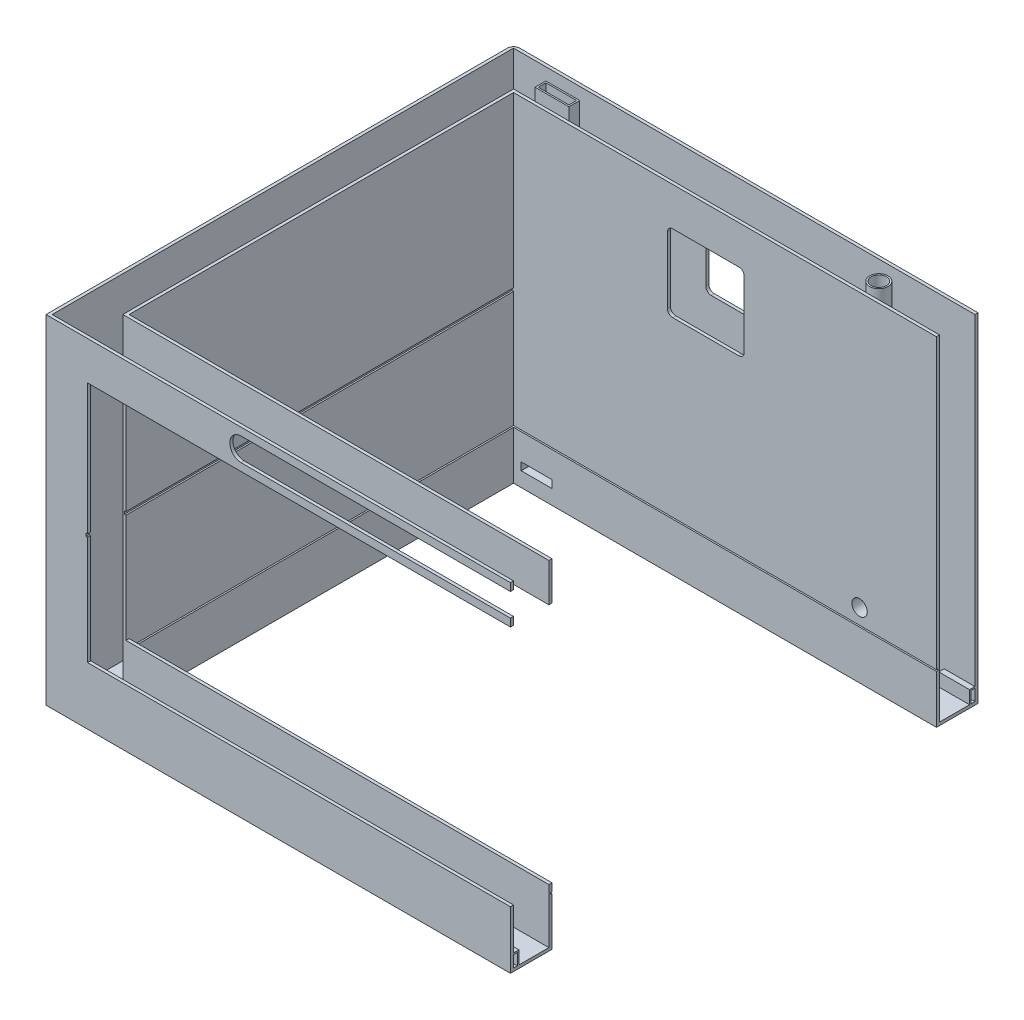
SolidWorks part; units mm, degrees
material "PVC Rigid"
ref_plane "Front Plane" through (0, 0, 0) normal (0, 0, 1) x (1, 0, 0)
ref_plane "Top Plane" through (0, 0, 0) normal (0, 1, 0) x (1, 0, 0)
ref_plane "Right Plane" through (0, 0, 0) normal (1, 0, 0) x (0, 0, -1)
sketch "Sketch1" plane through (0, 0, 0) normal (0, 1, 0) x (1, 0, 0)
  line L0 (0, -300) -> (0, 300) construction
  line L1 (0, 300) -> (-600, 300)
  line L2 (-600, 300) -> (-600, -300)
  line L3 (-600, -300) -> (0, -300)
  line L4 (0, -300) -> (0, -304)
  line L5 (0, -304) -> (-604, -304)
  line L6 (-604, -304) -> (-604, 304)
  line L7 (-604, 304) -> (0, 304)
  line L8 (0, 304) -> (0, 300)
  point P4 (0, 0)
extrude "Boss-Extrude1" add sketch "Sketch1" along normal blind 440
sketch "Sketch2" plane through (0, 0, 0) normal (0, 1, 0) x (1, 0, 0)
  line L0 (0, 0) -> (0, 250) construction
  line L1 (0, 250) -> (-550, 250)
  line L2 (-550, 250) -> (-550, -250)
  line L3 (-550, -250) -> (0, -250)
  line L4 (0, -250) -> (0, -254)
  line L5 (0, -254) -> (-554, -254)
  line L6 (-554, -254) -> (-554, 254)
  line L7 (-554, 254) -> (0, 254)
  line L8 (0, 254) -> (0, 250)
extrude "Boss-Extrude2" add sketch "Sketch2" along normal blind 440 separate body
sketch "Sketch3" plane through (0, 0, 0) normal (0, 1, 0) x (1, 0, 0)
  line L0 (0, -254) -> (0, -300)
  line L1 (0, -300) -> (-600, -300)
  line L2 (-600, -300) -> (-600, 300)
  line L3 (-600, 300) -> (0, 300)
  line L4 (0, 300) -> (0, 254)
  line L5 (0, 254) -> (-554, 254)
  line L6 (-554, 254) -> (-554, -254)
  line L7 (-554, -254) -> (0, -254)
extrude "Boss-Extrude3" add sketch "Sketch3" along normal blind 4
sketch "Sketch4" plane through (-550, 0, 0) normal (1, 0, 0) x (0, 0, -1)
  line L0 (0, 440) -> (0, 220) construction
  line L1 (-250, 440) -> (250, 440) construction
  line L2 (-250, 220) -> (250, 220)
  line L3 (250, 440) -> (250, 0) construction
  line L4 (-250, 220) -> (-250, 216)
  line L5 (-250, 440) -> (-250, 0) construction
  line L6 (-250, 216) -> (250, 216)
  line L7 (250, 216) -> (250, 220)
  line L8 (-250, 440) -> (-250, 0) construction
  point P10 (0, 220)
extrude "Cut-Extrude1" cut sketch "Sketch4" against normal blind 2
ref_plane "Plane1" through (0, 64, 0) normal (0, 1, 0) x (1, 0, 0)
sketch "Sketch7" plane through (0, 64, 0) normal (0, 1, 0) x (1, 0, 0)
  line L0 (-550, 250) -> (0, 250)
  line L1 (0, 250) -> (0, 252)
  line L2 (0, 250) -> (0, 254) construction
  line L3 (0, 252) -> (-552, 252)
  line L4 (-552, 252) -> (-552, -252)
  line L5 (-552, -252) -> (0, -252)
  line L6 (0, -254) -> (0, -250) construction
  line L7 (0, -252) -> (0, -250)
  line L8 (0, -250) -> (-550, -250)
  line L9 (-550, -250) -> (-550, 250)
extrude "Cut-Extrude3" cut sketch "Sketch7" against normal blind 1 and the other way blind 1
ref_plane "Plane2" through (0, 42, 0) normal (0, 1, 0) x (1, 0, 0)
sketch "Sketch10" plane through (0, 0, 304) normal (0, 0, 1) x (1, 0, 0)
  line L0 (0, 440) -> (0, 0) construction
  line L1 (-604, 440) -> (0, 440) construction
  line L2 (0, 390) -> (-550, 390)
  line L3 (-550, 390) -> (-550, 220)
  line L4 (-550, 220) -> (-552, 220)
  line L5 (-552, 220) -> (-552, 216)
  line L8 (-550, 75) -> (0, 75)
  line L9 (0, 75) -> (0, 390)
  line L10 (-552, 216) -> (-550, 216)
  line L11 (-550, 216) -> (-550, 75)
  point P0 (0, 390)
  dimension "D1" = 50
extrude "Cut-Extrude6" cut sketch "Sketch10" against normal up to vertex (54 mm away)
ref_plane "Plane3" through (0, 0, 0) normal (1, 0, 0) x (0, 0, -1)
sketch "Sketch11" plane through (0, 0, 0) normal (1, 0, 0) x (0, 0, -1)
  line L9 (-300, 4) -> (-254, 4) construction
  line L10 (-300, 75) -> (-300, 4) construction
  line L11 (-295, 4) -> (-295, 19)
  line L12 (-295, 19) -> (-300, 19)
  line L13 (-300, 19) -> (-300, 21)
  line L14 (-300, 440) -> (-300, 4) construction
  line L15 (-300, 21) -> (-293, 21)
  line L16 (-293, 21) -> (-293, 4)
  line L17 (-293, 4) -> (-295, 4)
  point P0 (-295, 4)
  dimension "D1" = 5
extrude "Boss-Extrude6" add sketch "Sketch11" against normal blind 40
sketch "Sketch12" plane through (0, 0, 0) normal (1, 0, 0) x (0, 0, -1)
  line L0 (254, 4) -> (300, 4) construction
  line L1 (300, 440) -> (300, 4) construction
  line L2 (295, 4) -> (293, 4)
  line L3 (300, 4) -> (-300, 4) construction
  line L4 (293, 4) -> (293, 21)
  line L5 (293, 21) -> (300, 21)
  line L6 (300, 21) -> (300, 19)
  line L7 (300, 19) -> (295, 19)
  line L8 (295, 19) -> (295, 4)
  point P0 (295, 4)
  dimension "D1" = 5
extrude "Boss-Extrude5" add sketch "Sketch12" against normal blind 40
sketch "Sketch13" plane through (0, 0, 304) normal (0, 0, 1) x (1, 0, 0)
  line L1 (0, 400) -> (0, 430)
  line L4 (0, 430) -> (-350, 430)
  line L9 (0, 440) -> (0, 390) construction
  line L10 (0, 400) -> (-350, 400)
  arc A0 (-350, 430) -> (-350, 400) centre (-350, 415) ccw
  point P5 (0, 415)
extrude "Cut-Extrude9" cut sketch "Sketch13" against normal blind 4 contours L4 A0 L10 L1
sketch "Sketch14" plane through (0, 0, -250) normal (0, 0, 1) x (1, 0, 0)
  line L0 (-550, 440) -> (0, 440) construction
  line L1 (-550, 440) -> (-550, 220) construction
  line L3 (-350, 290) -> (-250, 290)
  line L4 (-350, 290) -> (-350, 390)
  line L5 (-350, 390) -> (-250, 390)
  line L6 (-250, 290) -> (-250, 390)
  line L7 (-350, 290) -> (-250, 390) construction
  line L8 (-350, 390) -> (-250, 290) construction
  point P0 (-300, 340)
  point P5 (-300, 340)
  dimension "D1" = 100
  dimension "D2" = 250
extrude "Cut-Extrude10" cut sketch "Sketch14" against normal through all contours L5 L6 L3 L4
fillet "Fillet1" radius 7 8 edges at (-250, 290, -302) (-250, 290, -252) (-350, 290, -302) (-350, 290, -252) (-250, 390, -252) (-250, 390, -302) (-350, 390, -252) (-350, 390, -302)
fillet "Fillet2" radius 8 1 edges at (-604, 220, -304)
sketch "Sketch15" plane through (0, 0, 0) normal (0, -1, 0) x (1, 0, 0)
  line L0 (-604, -296) -> (-604, 304) construction
  line L1 (-604, 304) -> (0, 304) construction
  line L2 (-600, 300) -> (-600, 288)
  line L3 (-600, 288) -> (-598, 288)
  line L4 (-598, 288) -> (-598, 298)
  line L5 (-598, 298) -> (-588, 298)
  line L6 (-588, 298) -> (-588, 300)
  line L7 (-588, 300) -> (-600, 300)
  point P0 (-600, 300)
  dimension "D1" = 4
  dimension "D2" = 4
extrude "Cut-Extrude11" cut sketch "Sketch15" against normal blind 2 contours L7 L2 L3 L4 L5 L6
mirror "Mirror1" about plane through (0, 0, 0) normal (0, 0, 1) of "Cut-Extrude11"
sketch "Sketch16" plane through (-552, 0, 0) normal (1, 0, 0) x (0, 0, -1)
  line L0 (250, 220) -> (-254, 220) construction
  line L1 (-254, 218) -> (250, 218) construction
  line L2 (250, 216) -> (250, 220) construction
  line L3 (-254, 208) -> (250, 208) construction
  line L4 (-254, 216) -> (-254, 220) construction
  point P0 (-2, 218)
  point P8 (-2, 218)
  point P11 (-2, 208)
  dimension "D1" = 2
  dimension "D2" = 10
sketch "Sketch17" plane through (0, 4, 0) normal (0, 1, 0) x (1, 0, 0)
  line L0 (0, 300) -> (-600, 300) construction
  line L1 (-540, 282) -> (-500, 282)
  line L2 (-540, 282) -> (-540, 272)
  line L3 (-540, 272) -> (-500, 272)
  line L4 (-500, 282) -> (-500, 272)
  line L5 (-540, 282) -> (-500, 272) construction
  line L6 (-540, 272) -> (-500, 282) construction
  line L7 (-600, 300) -> (-600, -300) construction
  point P0 (-520, 277)
  dimension "D1" = 23
  dimension "D2" = 80
extrude "Cut-Extrude12" cut sketch "Sketch17" against normal blind 10
sketch "Sketch18" plane through (0, 4, 0) normal (0, 1, 0) x (1, 0, 0)
  line L0 (-540, 282) -> (-500, 282)
  line L1 (-500, 282) -> (-500, 272)
  line L2 (-500, 272) -> (-540, 272)
  line L3 (-540, 272) -> (-540, 282)
  line L4 (-520, 282) -> (-520, 284) construction
  line L5 (-542, 284) -> (-498, 284)
  line L6 (-498, 284) -> (-498, 270)
  line L7 (-498, 270) -> (-542, 270)
  line L8 (-542, 270) -> (-542, 284)
  point P12 (-520, 284)
extrude "Boss-Extrude7" add sketch "Sketch18" along normal up to surface (436 mm away) contours L3 L0 L1 L2 | L8 L5 L6 L7 up to face at (-333.9619, 440, -33.073)
sketch "Sketch19" plane through (0, 0, -270) normal (0, 0, 1) x (1, 0, 0)
  line L0 (-542, 440) -> (-542, 4) construction
  line L1 (-540, 29) -> (-500, 29)
  line L2 (-540, 29) -> (-540, 19)
  line L3 (-540, 19) -> (-500, 19)
  line L4 (-500, 29) -> (-500, 19)
  line L5 (-540, 29) -> (-500, 19) construction
  line L6 (-540, 19) -> (-500, 29) construction
  line L7 (-498, 4) -> (-542, 4) construction
  point P0 (-520, 24)
  dimension "D1" = 22
  dimension "D2" = 20
extrude "Cut-Extrude13" cut sketch "Sketch19" along normal up to surface and the other way blind 2 contours L1 L4 L3 L2 up to face at (-413, 235.25, -250)
sketch "Sketch20" plane through (0, 0, -270) normal (0, 0, 1) x (1, 0, 0)
  line L0 (-540, 29) -> (-500, 29)
  line L1 (-500, 29) -> (-500, 19)
  line L2 (-500, 19) -> (-540, 19)
  line L3 (-540, 19) -> (-540, 29)
  line L4 (-520, 29) -> (-520, 31) construction
  line L5 (-542, 31) -> (-498, 31)
  line L6 (-498, 440) -> (-498, 4) construction
  line L7 (-542, 31) -> (-542, 17)
  line L8 (-542, 440) -> (-542, 4) construction
  line L9 (-542, 17) -> (-498, 17)
  line L10 (-498, 17) -> (-498, 31)
  point P14 (-520, 31)
extrude "Boss-Extrude8" add sketch "Sketch20" along normal blind 16 contours L3 L0 L1 L2 | L7 L9 L10 L5
sketch "Sketch21" plane through (0, 0, -250) normal (0, 0, 1) x (1, 0, 0)
  line L0 (-550, 65) -> (0, 65) construction
  line L1 (-550, 216) -> (-550, 65) construction
  circle A0 centre (-100, 85) radius 10
  dimension "D1" = 20
  dimension "D2" = 450
extrude "Cut-Extrude14" cut sketch "Sketch21" against normal blind 25
sketch "Sketch25" plane through (0, 0, -254) normal (0, 0, -1) x (-1, 0, 0)
  circle A0 centre (100, 85) radius 10
  circle A1 centre (100, 85) radius 12
extrude "Boss-Extrude10" add sketch "Sketch25" along normal blind 17
sketch "Sketch22" plane through (0, 4, 0) normal (0, 1, 0) x (1, 0, 0)
  line L2 (0, 254) -> (0, 293) construction
  line L3 (0, 300) -> (-600, 300) construction
  circle A0 centre (-100, 275) radius 10
  dimension "D1" = 100
  dimension "D2" = 25
extrude "Cut-Extrude15" cut sketch "Sketch22" against normal up to surface (4 mm away) contours A0 up to face at (-520, 0, -277)
sketch "Sketch23" plane through (0, 4, 0) normal (0, 1, 0) x (1, 0, 0)
  circle A0 centre (-100, 275) radius 10
  circle A1 centre (-100, 275) radius 12
extrude "Boss-Extrude9" add sketch "Sketch23" along normal up to surface (436 mm away) contours A0 | A1 up to face at (-333.9619, 440, -33.073)
